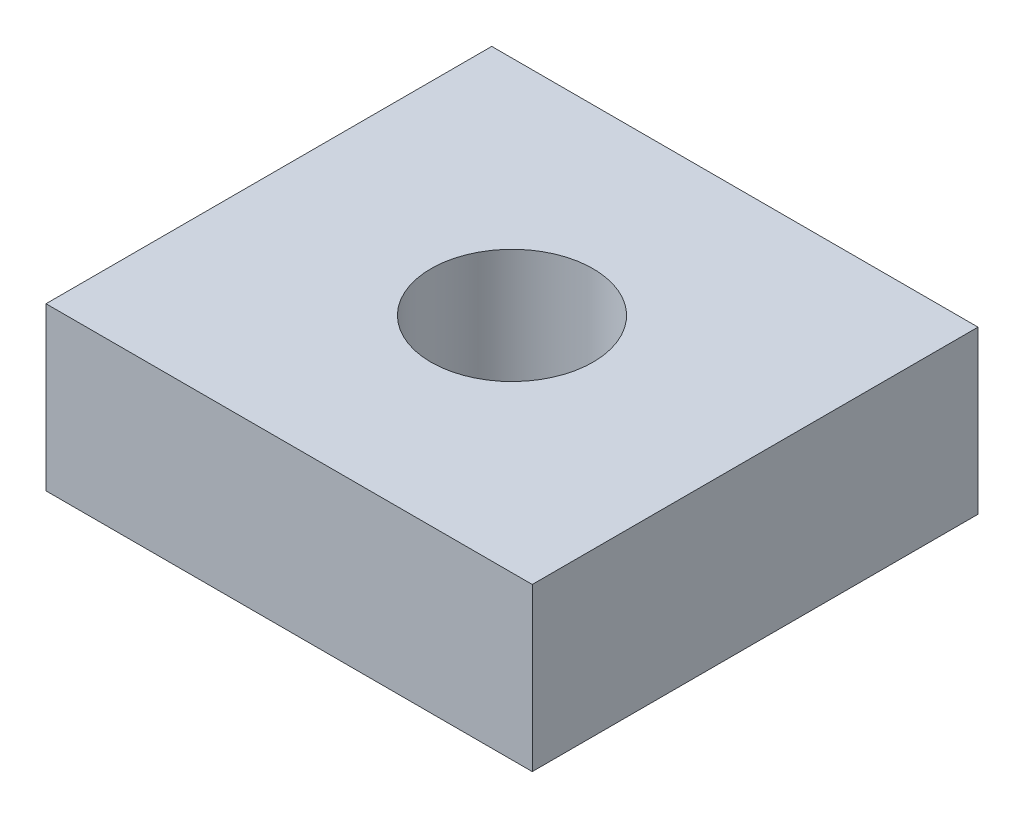
SolidWorks part; units mm, degrees
ref_plane "Front Plane" through (0, 0, 0) normal (0, 0, 1) x (1, 0, 0)
ref_plane "Top Plane" through (0, 0, 0) normal (0, 1, 0) x (1, 0, 0)
ref_plane "Right Plane" through (0, 0, 0) normal (1, 0, 0) x (0, 0, -1)
sketch "Sketch1" plane through (0, 0, 0) normal (0, 1, 0) x (1, 0, 0)
  line L1 (-38.1, -34.925) -> (38.1, -34.925)
  line L2 (-38.1, -34.925) -> (-38.1, 34.925)
  line L3 (-38.1, 34.925) -> (38.1, 34.925)
  line L4 (38.1, -34.925) -> (38.1, 34.925)
  line L5 (-38.1, -34.925) -> (38.1, 34.925) construction
  line L6 (-38.1, 34.925) -> (38.1, -34.925) construction
  point P0 (0, 0)
  dimension "D1" = 76.2
  dimension "D2" = 69.85
extrude "Boss-Extrude1" add sketch "Sketch1" along normal blind 25.4
sketch "Sketch2" plane through (0, 25.4, 0) normal (0, 1, 0) x (1, 0, 0)
  circle A0 centre (0, 0) radius 12.7
  dimension "D1" = 25.4
extrude "Cut-Extrude1" cut sketch "Sketch2" against normal through all
